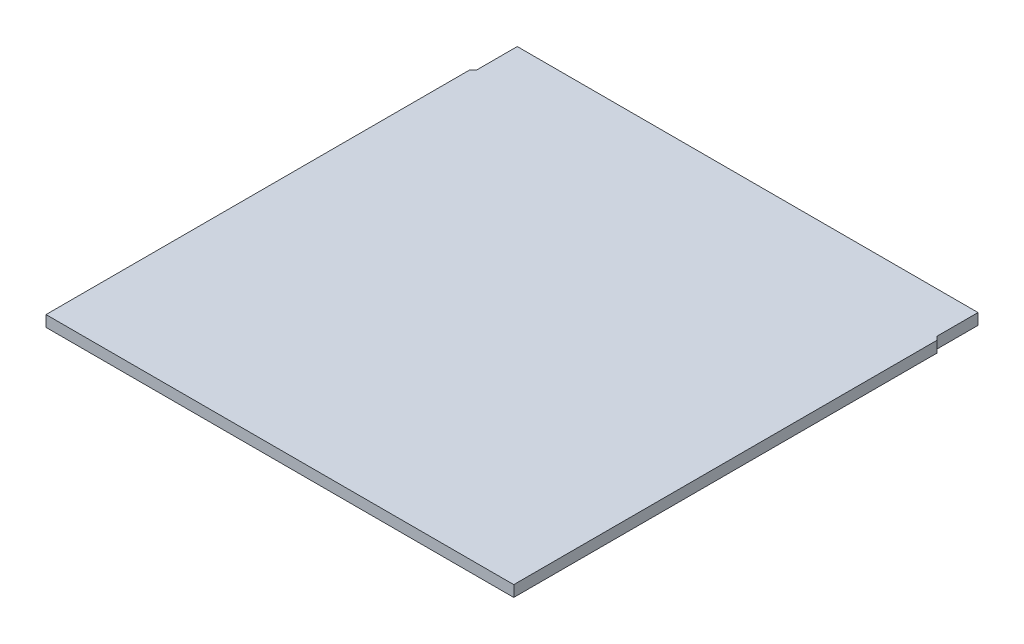
SolidWorks part; units mm, degrees
ref_plane "Front Plane" through (0, 0, 0) normal (0, 0, 1) x (1, 0, 0)
ref_plane "Top Plane" through (0, 0, 0) normal (0, 1, 0) x (1, 0, 0)
ref_plane "Right Plane" through (0, 0, 0) normal (1, 0, 0) x (0, 0, -1)
sketch "Sketch1" plane through (0, 0, 0) normal (0, 1, 0) x (1, 0, 0)
  line L1 (200, 200) -> (-200, 200)
  line L2 (200, 200) -> (200, -200)
  line L3 (200, -200) -> (-200, -200)
  line L4 (-200, 200) -> (-200, -200)
  line L5 (200, 200) -> (-200, -200) construction
  line L6 (200, -200) -> (-200, 200) construction
  point P0 (0, 0)
  dimension "D1" = 400
  dimension "D2" = 400
extrude "Boss-Extrude1" add sketch "Sketch1" along normal blind 9.525
sketch "Sketch2" plane through (0, 9.525, 0) normal (0, 1, 0) x (1, 0, 0)
  line L0 (197, 200) -> (197, 165)
  line L1 (200, 200) -> (-200, 200) construction
  line L2 (197, 165) -> (200, 162)
  line L3 (200, -200) -> (200, 200) construction
  line L4 (200, 162) -> (200, 200)
  line L5 (200, 200) -> (197, 200)
  dimension "D1" = 3
  dimension "D2" = 45
  dimension "D3" = 35
extrude "Cut-Extrude1" cut sketch "Sketch2" against normal through all
mirror "Mirror1" about plane through (0, 0, 0) normal (1, 0, 0) of "Cut-Extrude1"
